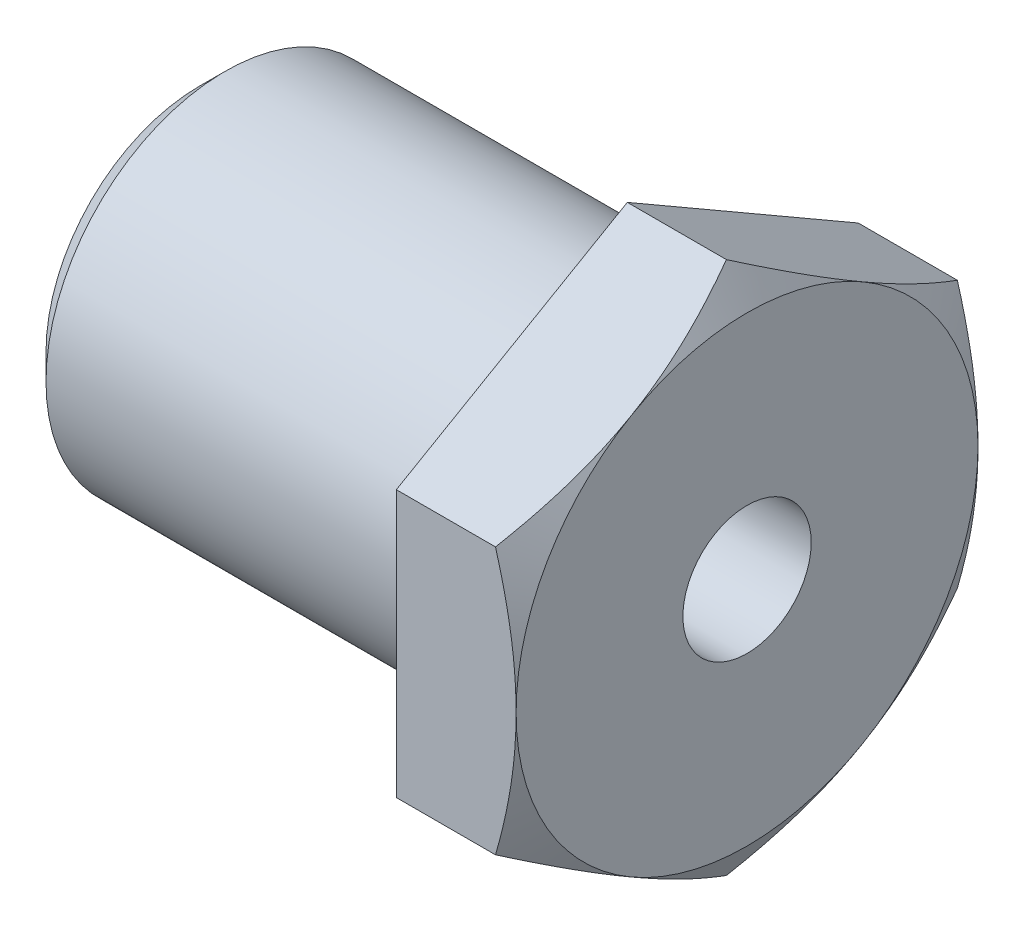
SolidWorks part; units mm, degrees
ref_plane "Płaszczyzna przednia" through (0, 0, 0) normal (0, 0, 1) x (1, 0, 0)
ref_plane "Płaszczyzna górna" through (0, 0, 0) normal (0, 1, 0) x (1, 0, 0)
ref_plane "Płaszczyzna prawa" through (0, 0, 0) normal (1, 0, 0) x (0, 0, -1)
sketch "Szkic1" plane through (0, 0, 0) normal (1, 0, 0) x (0, 0, -1)
  line L1 (13.5, 7.7942) -> (0, 15.5885)
  line L2 (0, 15.5885) -> (-13.5, 7.7942)
  line L3 (-13.5, 7.7942) -> (-13.5, -7.7942)
  line L4 (-13.5, -7.7942) -> (0, -15.5885)
  line L5 (0, -15.5885) -> (13.5, -7.7942)
  line L6 (13.5, -7.7942) -> (13.5, 7.7942)
  circle A0 centre (0, 0) radius 13.5 construction
  dimension "D1" = 27
extrude "Dodanie-wyciągnięcie1" add sketch "Szkic1" against normal blind 7
sketch "Szkic2" plane through (0, 0, 0) normal (1, 0, 0) x (0, 0, -1)
  circle A0 centre (0, 0) radius 13.5
  dimension "D1" = 27
extrude "Wytnij-wyciągnięcie1" cut sketch "Szkic2" against normal blind 7 draft 60 flip side to cut
sketch "Szkic3" plane through (-7, 0, 0) normal (-1, 0, 0) x (0, 0, 1)
  circle A0 centre (0, 0) radius 10.48
  dimension "D1" = 20.96
extrude "Dodanie-wyciągnięcie2" add sketch "Szkic3" along normal blind 25
sketch "Szkic4" plane through (-32, 0, 0) normal (-1, 0, 0) x (0, 0, 1)
  circle A0 centre (0, 0) radius 7.25
  dimension "D1" = 14.5
extrude "Wytnij-wyciągnięcie2" cut sketch "Szkic4" against normal blind 20
sketch "Szkic5" plane through (0, 0, 0) normal (1, 0, 0) x (0, 0, -1)
  circle A0 centre (0, 0) radius 3.75
  dimension "D1" = 7.5
extrude "Wytnij-wyciągnięcie3" cut sketch "Szkic5" against normal up to surface (12 mm away) up to face at (-12, 0, 7.25)
chamfer "Sfazowanie1" distance 1.5 angle 45 1 edges at (-32, 0, 10.48)
sketch "Szkic6" plane through (0, 0, 0) normal (0, 0, 1) x (1, 0, 0)
  line L0 (-7, 10.48) -> (-7, -10.48) construction
  line L1 (-9, 10) -> (-9, 11.5)
  line L2 (-9, 11.5) -> (-7, 11.5)
  line L3 (-7, 11.5) -> (-7, 10)
  line L4 (0, 0) -> (-23.3124, 0) construction
  arc A0 (-9, 10) -> (-7, 10) centre (-8, 10) ccw
  point P2 (-8, 9)
  dimension "D1" = 2
  dimension "D2" = 18
  dimension "D3" = 1.5
revolve "Wycięcie-obrót1" cut sketch "Szkic6" angle 360 about L4
